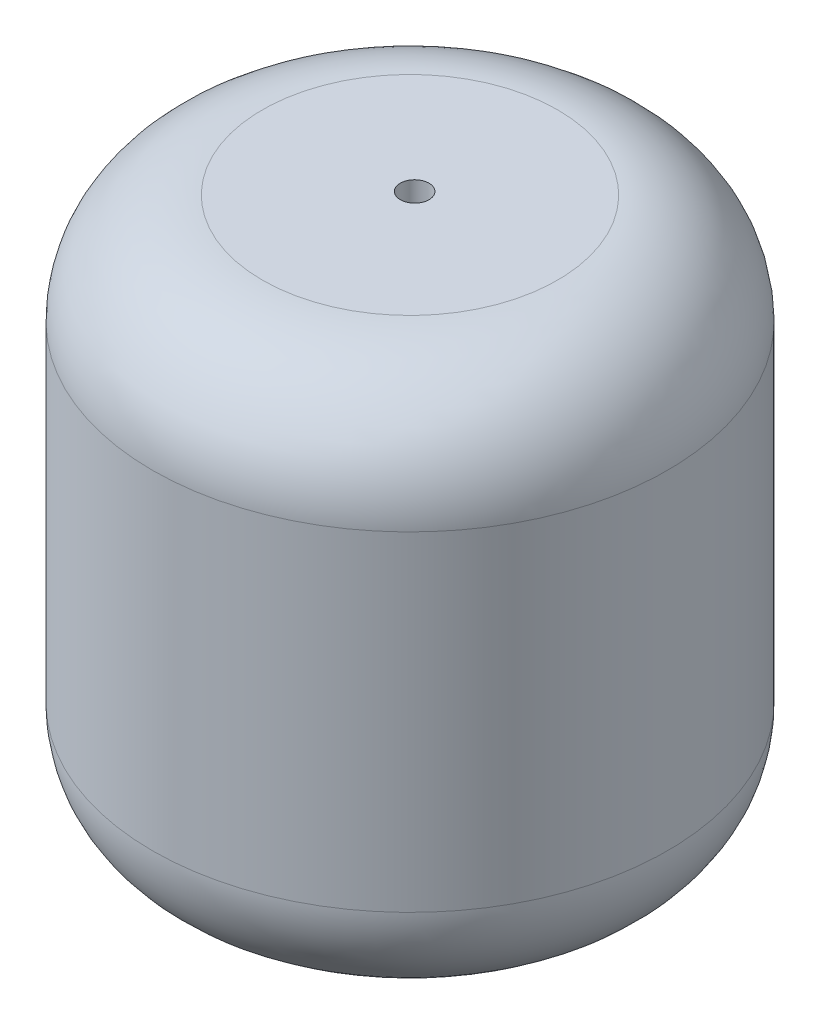
SolidWorks part; units mm, degrees
ref_plane "Front Plane" through (0, 0, 0) normal (0, 0, 1) x (1, 0, 0)
ref_plane "Top Plane" through (0, 0, 0) normal (0, 1, 0) x (1, 0, 0)
ref_plane "Right Plane" through (0, 0, 0) normal (1, 0, 0) x (0, 0, -1)
sketch "Sketch1" plane through (0, 0, 0) normal (0, 1, 0) x (1, 0, 0)
  circle A0 centre (-4.8001, 11.467) radius 11.9062
  dimension "D1" = 23.8125
extrude "Boss-Extrude1" add sketch "Sketch1" along normal blind 25.4
fillet "Fillet3" radius 5.08 1 edges at (-4.8001, 25.4, 0.4393)
fillet "Fillet4" radius 5.08 1 edges at (-4.8001, 0, 0.4393)
sketch "Sketch2" plane through (0, 25.4, 0) normal (0, 1, 0) x (1, 0, 0)
  circle A0 centre (-4.8333, 11.716) radius 0.6642
  point P2 (0, 0)
  point P3 (0, 0)
extrude "Cut-Extrude1" cut sketch "Sketch2" against normal blind 25.4
